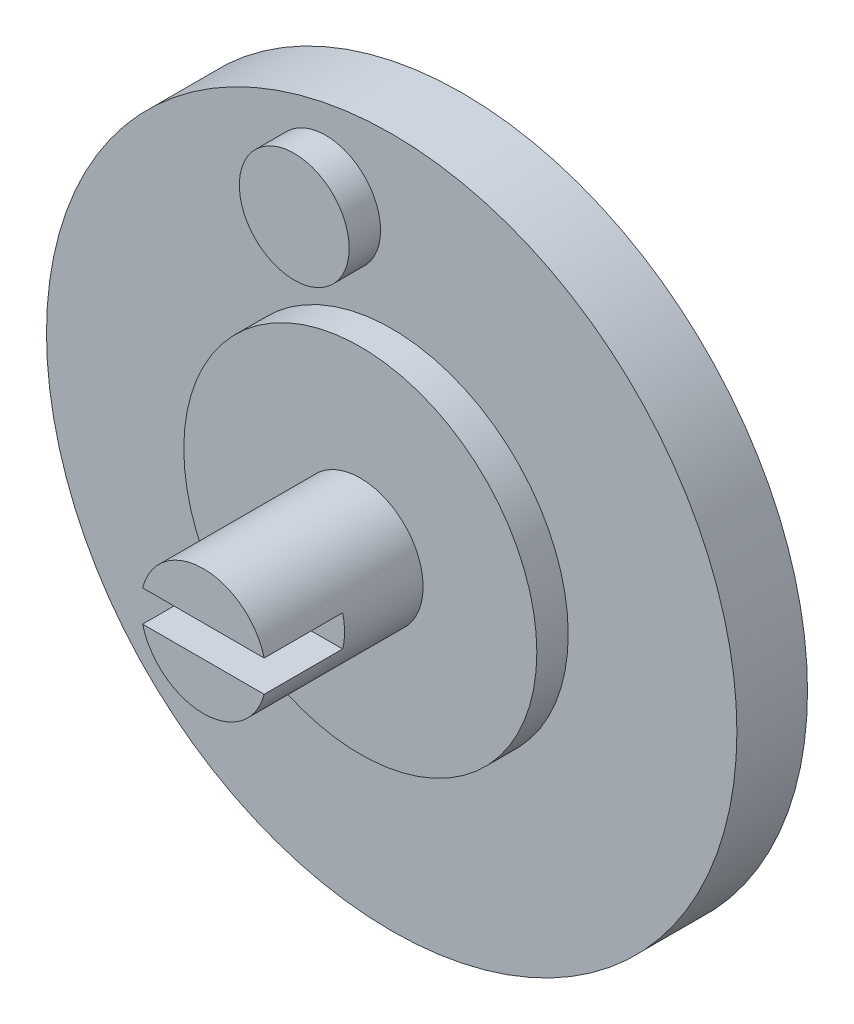
SolidWorks part; units mm, degrees
ref_plane "Front Plane" through (0, 0, 0) normal (0, 0, 1) x (1, 0, 0)
ref_plane "Top Plane" through (0, 0, 0) normal (0, 1, 0) x (1, 0, 0)
ref_plane "Right Plane" through (0, 0, 0) normal (1, 0, 0) x (0, 0, -1)
sketch "Sketch1" plane through (0, 0, 0) normal (0, 0, 1) x (1, 0, 0)
  circle A0 centre (0, 0) radius 22
  dimension "D1" = 44
extrude "Boss-Extrude1" add sketch "Sketch1" along normal blind 4.5
sketch "Sketch2" plane through (0, 0, 0) normal (0, 0, 1) x (1, 0, 0)
  circle A0 centre (0, 0) radius 11.25
  dimension "D1" = 22.5
extrude "Boss-Extrude2" add sketch "Sketch2" along normal blind 2 from surface at 4.5 starting at face at (22, 0, 4.5)
sketch "Sketch3" plane through (0, 0, 0) normal (0, 0, 1) x (1, 0, 0)
  circle A0 centre (0, 0) radius 16.85 construction
  circle A1 centre (-4.2104, 16.3155) radius 3.5
  dimension "D1" = 33.7
  dimension "D2" = 7
extrude "Boss-Extrude3" add sketch "Sketch3" along normal blind 2 from surface at 4.5 starting at face at (11.25, 0, 4.5)
sketch "Sketch4" plane through (0, 0, 0) normal (0, 0, 1) x (1, 0, 0)
  circle A0 centre (0, 0) radius 4
  dimension "D1" = 8
extrude "Boss-Extrude4" add sketch "Sketch4" along normal blind 10 from surface at 6.5 starting at face at (11.25, 0, 6.5)
sketch "Sketch5" plane through (0, 0, 0) normal (0, 0, 1) x (1, 0, 0)
  line L0 (-24.8674, 1) -> (29.4205, 1)
  line L1 (-24.8674, -1) -> (29.4205, -1)
  line L2 (29.4205, -1) -> (29.4205, 1)
  line L3 (-24.8674, 1) -> (-24.8674, -1)
  dimension "D1" = 2
  dimension "D2" = 1
extrude "Cut-Extrude1" cut sketch "Sketch5" against normal blind 5 from surface at 16.5 starting at face at (4, 0, 16.5)
sketch "Sketch6" plane through (0, 0, 0) normal (0, 0, 1) x (1, 0, 0)
  circle A0 centre (0, 0) radius 13
  dimension "D1" = 26
extrude "Cut-Extrude2" cut sketch "Sketch6" along normal blind 4 from surface at 0 starting at face at (22, 0, 0)
